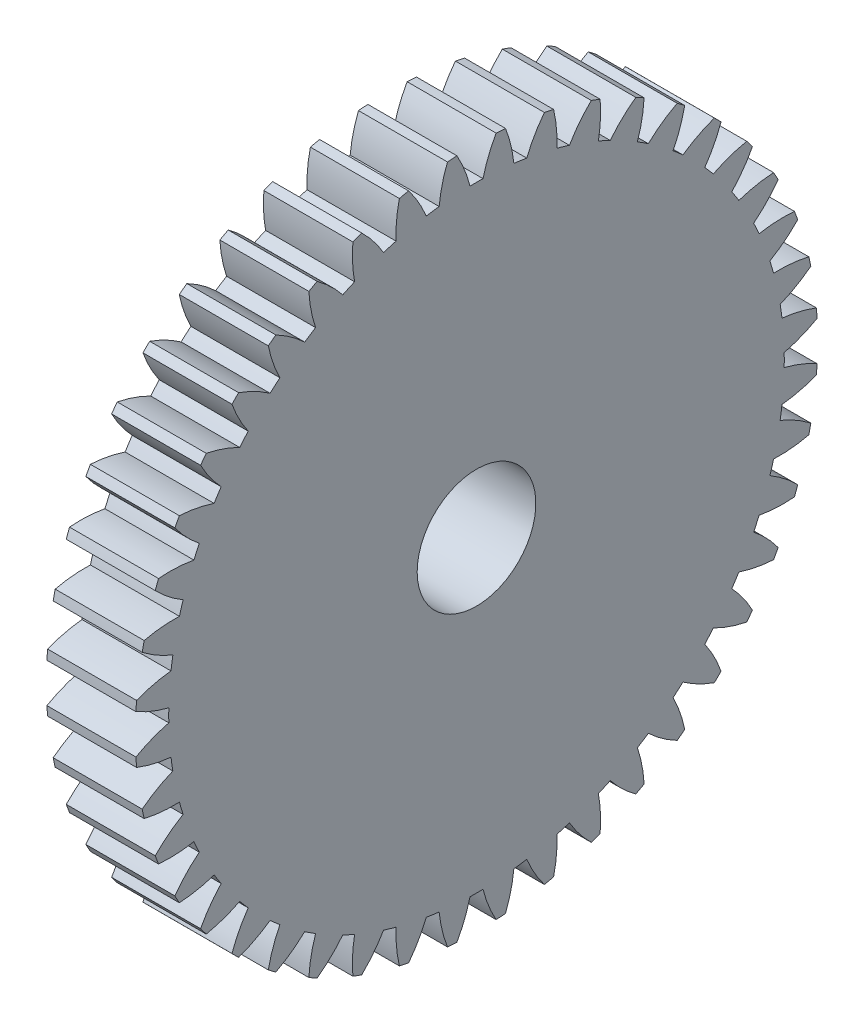
SolidWorks part; units mm, degrees
ref_plane "Plane1" through (0, 0, 0) normal (0, 0, 1) x (1, 0, 0)
ref_plane "Plane2" through (0, 0, 0) normal (0, 1, 0) x (1, 0, 0)
ref_plane "Plane3" through (0, 0, 0) normal (1, 0, 0) x (0, 0, -1)
sketch "HoldingSke" plane through (0, 0, 0) normal (0, 1, 0) x (1, 0, 0)
  line L0 (0, 0) -> (0.2877, -0.2779)
  line L1 (-15, 0) -> (100, 0) construction
  line L2 (0, 0) -> (-2.1039, 2.3779)
  line L3 (0, 0) -> (-11.863, 4.5341)
  line L4 (0, 0) -> (6.2122, 5.9991)
  line L5 (0, 0) -> (-46.8476, -17.4728)
  line L6 (0, 0) -> (-12.4344, -8.3896)
  line L7 (-2.1039, 2.3779) -> (8.6586, 51.2059)
  line L8 (-76.2, 54.61) -> (-73.4, 54.61)
  line L9 (-71.009, 38.7566) -> (-53.1078, 45.2721)
  line L10 (-76.2, 71.12) -> (104.1128, 71.12)
  line L11 (0, 0) -> (-15, 0)
  line L12 (-76.2, 101.6) -> (-76.113, 101.6)
  line L13 (24.9733, 27.94) -> (52.9518, 28.4284)
  line L14 (24.9733, 27.94) -> (24.9743, 27.94)
  line L15 (24.9733, 27.94) -> (100.4006, 29.5858)
  line L16 (-63.627, -2.5) -> (-12.827, -2.5)
  circle A0 centre (0, 0) radius 10
  circle A1 centre (0, 0) radius 37.5
  circle A2 centre (0, 0) radius 37.5
  circle A3 centre (0, 0) radius 10
  dimension "MHD" = 75
  dimension "Hub_dia" = 75
  dimension "Bore" = 20
  dimension "MBD" = 20
  dimension "Num_teeth" = 44
  dimension "Pitch" = 0.4
  dimension "Overall_len" = 50
  dimension "Show_teeth" = 44
  dimension "Thickness" = 15
  dimension "OAL" = 50.0001
  dimension "T_dim" = 2.8
  dimension "Ap" = 20
  dimension "H" = 19.05
  dimension "Pitch_radius" = 180.3128
  dimension "Width" = 15
  dimension "Backlash" = 0.087
  dimension "Addendum_fac" = 1
  dimension "Dedendum_fac" = 1.25
  dimension "Clearance_fac" = 0.25
  dimension "Dedendum_add" = 0.001
  dimension "Module" = 2.5
sketch "BasProSke" plane through (0, 0, 0) normal (0, 1, 0) x (1, 0, 0)
  line L0 (-10, 0) -> (60, 0) construction
  line L1 (0, 0) -> (0, 57.5)
  line L2 (0, 0) -> (15, 0)
  line L3 (15, 0) -> (15, 57.5)
  line L4 (15, 57.5) -> (0, 57.5)
  dimension "Thickness" = 15
  dimension "Diameter" = 115
revolve "Base-Revolve" add sketch "BasProSke" angle 360 about L0
sketch "TooCutSke" plane through (0, 0, 0) normal (1, 0, 0) x (0, 0, -1)
  line L1 (0, 0) -> (0, 107) construction
  line L2 (0, 0) -> (-2.1153, 54.9593) construction
  line L3 (0, 0) -> (-7.8431, 109.6602) construction
  line L4 (-2.1153, 54.9593) -> (-3.9215, 54.8301) construction
  arc A0 (1.0964, 51.8624) -> (-1.0964, 51.8624) centre (0, 0) ccw
  arc A1 (3.3223, 57.4294) -> (-3.3223, 57.4294) centre (0, 0) ccw
  circle A2 centre (0, 0) radius 55 construction
  circle A3 centre (0, 0) radius 51.6831 construction
  arc A4 (-1.0964, 51.8624) -> (-3.3223, 57.4294) centre (-22.4465, 46.5543) ccw
  arc A5 (3.3223, 57.4294) -> (1.0964, 51.8624) centre (22.4465, 46.5543) ccw
  dimension "Root_dia" = 103.748
  dimension "Overcut_dia" = 115.0508
  dimension "Pitch_dia" = 110
  dimension "Base_dia" = 103.3662
  dimension "Flank_rad" = 22
  dimension "Half_ang" = 4.091
  dimension "Half_CT" = 1.8108
extrude "ToothCut" cut sketch "TooCutSke" along normal through all
fillet "Breaks" [suppressed] radius 0.05
fillet "RootFillets" [suppressed] radius 0.626
pattern_circular "TeethCuts" count 44 every 8.182 about axis through (-10, 0, 0) along (1, 0, 0) of "ToothCut", "RootFillets", "Breaks"
sketch "HubNeaOneSke" plane through (0, 0, 0) normal (-1, 0, 0) x (0, 0, 1)
  circle A0 centre (0, 0) radius 37.5
  dimension "Diameter" = 75
extrude "HubNearOne" [suppressed] add sketch "HubNeaOneSke" along normal blind 35.0001
sketch "HubNeaBotSke" plane through (0, 0, 0) normal (-1, 0, 0) x (0, 0, 1)
  circle A0 centre (0, 0) radius 37.5
  dimension "Diameter" = 75
extrude "HubNearBoth" [suppressed] add sketch "HubNeaBotSke" along normal blind 17.5
ref_plane "FarPln" through (15, 0, 0) normal (1, 0, 0) x (0, 0, -1)
sketch "HubFarSke" plane through (15, 0, 0) normal (1, 0, 0) x (0, 0, -1)
  circle A0 centre (0, 0) radius 37.5
  dimension "Diameter" = 75
extrude "HubFar" [suppressed] add sketch "HubFarSke" along normal blind 17.5
sketch "BorSke" plane through (0, 0, 0) normal (1, 0, 0) x (0, 0, -1)
  circle A0 centre (0, 0) radius 10
  dimension "Diameter" = 20
extrude "Bore" cut sketch "BorSke" along normal mid plane 100.0001
sketch "KeySke" plane through (0, 0, 0) normal (1, 0, 0) x (0, 0, -1)
  line L0 (-3, 0) -> (-3, 12.8)
  line L1 (-3, 12.8) -> (3, 12.8)
  line L2 (3, 12.8) -> (3, 0)
  line L3 (0, 0) -> (0, 34) construction
  line L4 (-3, 0) -> (3, 0)
  dimension "Offset" = 12.8
  dimension "Width" = 6
extrude "Keyway" [suppressed] cut sketch "KeySke" along normal mid plane 100.0001
pattern_circular "Keyway2" [suppressed] count 2 every 90 about axis through (-10, 0, 0) along (1, 0, 0)
equation "' \"Module@HoldingSke\" = 6.35"
equation "' \"Num_teeth@HoldingSke\" = 12"
equation "' \"Ap@HoldingSke\" =  20"
equation "' \"Ap@HoldingSke\" = 20"
equation "' \"Width@HoldingSke\" = 0.5 * 25.4"
equation "' \"Hub_dia@HoldingSke\"= 1 * 25.4"
equation "' \"Hub_dia@HoldingSke\" = 1 * 25.4"
equation "' \"Overall_len@HoldingSke\" = 1.0 * 25.4"
equation "' \"Bore@HoldingSke\" = 0.75 * 25.4"
equation "' \"T_dim@HoldingSke\" = 0.1 * 25.4"
equation "' \"Width@KeySke\" = 0.25 * 25.4"
equation "' \"Show_teeth@HoldingSke\" = 13"
equation "' \"Backlash@HoldingSke\" = 0.009 * 25.4"
equation "' \"Addendum_fac@HoldingSke\" = 1.0"
equation "' \"Dedendum_fac@HoldingSke\" = 1.25"
equation "' \"Dedendum_add@HoldingSke\" = 0.00005 * 25.4"
equation "' \"Clearance_fac@HoldingSke\" = 0.25"
equation "\"Pitch@HoldingSke\" = 1 / \"Module@HoldingSke\""
equation "\"Overcut_dia@TooCutSke\" = (\"Num_teeth@HoldingSke\" + 2 * \"Addendum_fac@HoldingSke\") / \"Pitch@HoldingSke\" + 0.002 * 25.4"
equation "\"Pitch_dia@TooCutSke\" = \"Num_teeth@HoldingSke\" / \"Pitch@HoldingSke\""
equation "\"Base_dia@TooCutSke\" = \"Num_teeth@HoldingSke\" / \"Pitch@HoldingSke\" * cos((\"Ap@HoldingSke\"  * 3.14159265 / 180))"
equation "\"Root_dia@TooCutSke\" = (\"Num_teeth@HoldingSke\" + 2) / \"Pitch@HoldingSke\" - 2 * (\"Addendum_fac@HoldingSke\" + \"Dedendum_fac@HoldingSke\") / \"Pitch@HoldingSke\" - \"Dedendum_add@HoldingSke\" * 2"
equation "\"Half_ang@TooCutSke\" = 180 / \"Num_teeth@HoldingSke\""
equation "\"Half_CT@TooCutSke\" = \"Num_teeth@HoldingSke\" / \"Pitch@HoldingSke\" * sin((3.14159265 / 2 / \"Num_teeth@HoldingSke\")) / 2 - 7 * \"Backlash@HoldingSke\" / 4"
equation "\"Flank_rad@TooCutSke\" = \"Num_teeth@HoldingSke\" / \"Pitch@HoldingSke\" / 5"
equation "\"Radius@RootFillets\" = \"Clearance_fac@HoldingSke\" / \"Pitch@HoldingSke\" + \"Dedendum_add@HoldingSke\""
equation "\"Break_rad@Breaks\" = 0.02 / \"Pitch@HoldingSke\""
equation "\"Thickness@HoldingSke\" = \"Width@HoldingSke\""
equation "\"OAL@HoldingSke\" = \"Thickness@HoldingSke\""
equation "\"MHD@HoldingSke\" = (\"Num_teeth@HoldingSke\" + 2) / \"Pitch@HoldingSke\" - 2 * (\"Addendum_fac@HoldingSke\" + \"Dedendum_fac@HoldingSke\")  / \"Pitch@HoldingSke\" - \"Dedendum_add@HoldingSke\" * 2"
equation "\"MBD@HoldingSke\" = (\"Num_teeth@HoldingSke\" + 2) / \"Pitch@HoldingSke\" - 2 * (\"Addendum_fac@HoldingSke\" + \"Dedendum_fac@HoldingSke\")  / \"Pitch@HoldingSke\" - \"Dedendum_add@HoldingSke\" * 2 - 0.002 * 25.4"
equation "\"MHD@HoldingSke\" = ((sgn( \"MHD@HoldingSke\" - \"Hub_dia@HoldingSke\" )-1)*( \"MHD@HoldingSke\" - \"Hub_dia@HoldingSke\" ))/-2+ \"Hub_dia@HoldingSke\""
equation "\"MBD@HoldingSke\" = ((sgn( \"MBD@HoldingSke\" - \"Bore@HoldingSke\" )-1)*( \"MBD@HoldingSke\" - \"Bore@HoldingSke\" ))/-2+ \"Bore@HoldingSke\""
equation "\"OAL@HoldingSke\" = ((sgn( \"OAL@HoldingSke\" - \"Overall_len@HoldingSke\" )+1)*( \"OAL@HoldingSke\" - \"Overall_len@HoldingSke\" ))/2 + \"Overall_len@HoldingSke\" + 0.000002 * 25.4"
equation "\"Num_teeth@TeethCuts\" = int( \"Show_teeth@HoldingSke\" ) + 1"
equation "\"Num_teeth@TeethCuts\" = ((sgn( \"Num_teeth@TeethCuts\" - \"Num_teeth@HoldingSke\" )-1)*( \"Num_teeth@TeethCuts\" - \"Num_teeth@HoldingSke\" ))/-2+ \"Num_teeth@HoldingSke\""
equation "\"Num_teeth@TeethCuts\" = ((sgn( \"Num_teeth@TeethCuts\" - 2.0)+1)*( \"Num_teeth@TeethCuts\" - 2.0))/2 +2.0"
equation "\"Angle@TeethCuts\" = 360.0 / \"Num_teeth@HoldingSke\""
equation "\"Diameter@BasProSke\" = (\"Num_teeth@HoldingSke\" + 2 * \"Addendum_fac@HoldingSke\") / \"Pitch@HoldingSke\""
equation "\"Thickness@BasProSke\"  = \"Thickness@HoldingSke\""
equation "' \"Fillet_rad@BasProSke\" =  \"Thickness@HoldingSke\" * 0.05"
equation "' \"Fillet_rad@BasProSke\" = \"Thickness@HoldingSke\" * 0.05"
equation "\"MHD@HoldingSke\" = ((sgn( \"MHD@HoldingSke\" - \"Root_dia@TooCutSke\" )-1)*( \"MHD@HoldingSke\" - \"Root_dia@TooCutSke\" ))/-2+ \"Root_dia@TooCutSke\""
equation "\"Diameter@HubNeaOneSke\" = \"MHD@HoldingSke\""
equation "\"Length@HubNearOne\" = \"OAL@HoldingSke\" - \"Thickness@BasProSke\""
equation "\"Diameter@HubNeaBotSke\" = \"MHD@HoldingSke\""
equation "\"Length@HubNearBoth\" = ( \"OAL@HoldingSke\" - \"Thickness@BasProSke\" ) / 2.0"
equation "\"Thickness@FarPln\" = \"Thickness@BasProSke\""
equation "\"Diameter@HubFarSke\" = \"MHD@HoldingSke\""
equation "\"Length@HubFar\" = ( \"OAL@HoldingSke\" - \"Thickness@BasProSke\" ) / 2.0"
equation "\"Diameter@BorSke\" = \"MBD@HoldingSke\""
equation "\"D1@Bore\" = \"OAL@HoldingSke\" * 2.0"
equation "\"D1@Keyway\" = \"OAL@HoldingSke\" * 2.0"
equation "\"Offset@KeySke\" = \"T_dim@HoldingSke\" + \"MBD@HoldingSke\" / 2.0"
